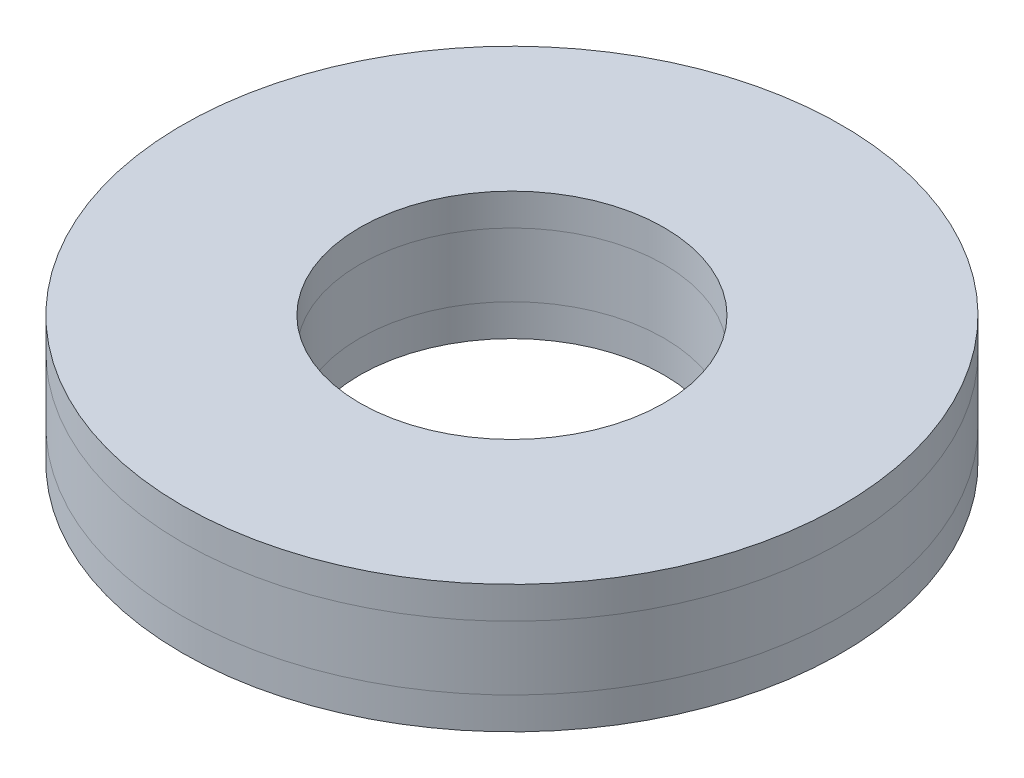
SolidWorks part; units mm, degrees
ref_plane "Front Plane" through (0, 0, 0) normal (0, 0, 1) x (1, 0, 0)
ref_plane "Top Plane" through (0, 0, 0) normal (0, 1, 0) x (1, 0, 0)
ref_plane "Right Plane" through (0, 0, 0) normal (1, 0, 0) x (0, 0, -1)
sketch "Sketch1" plane through (0, 0, 0) normal (0, 1, 0) x (1, 0, 0)
  circle A0 centre (0, 0) radius 10.32
  circle A1 centre (0, 0) radius 4.7625
  dimension "D1" = 9.525
  dimension "D2" = 20.64
extrude "Boss-Extrude1" add sketch "Sketch1" along normal blind 1
sketch "Sketch2" plane through (0, 1, 0) normal (0, 1, 0) x (1, 0, 0)
  circle A0 centre (0, 0) radius 4.7625 construction
  circle A1 centre (0, 0) radius 10.32
  circle A2 centre (0, 0) radius 10.32
  circle A3 centre (0, 0) radius 4.7625
  dimension "D1" = 0
extrude "Boss-Extrude2" add sketch "Sketch2" along normal blind 2 separate body
sketch "Sketch3" plane through (0, 3, 0) normal (0, 1, 0) x (1, 0, 0)
  circle A0 centre (0, 0) radius 4.7625 construction
  circle A1 centre (0, 0) radius 10.32
  circle A2 centre (0, 0) radius 10.32
  circle A3 centre (0, 0) radius 4.7625
  dimension "D1" = 0
extrude "Boss-Extrude3" add sketch "Sketch3" along normal blind 1 separate body
